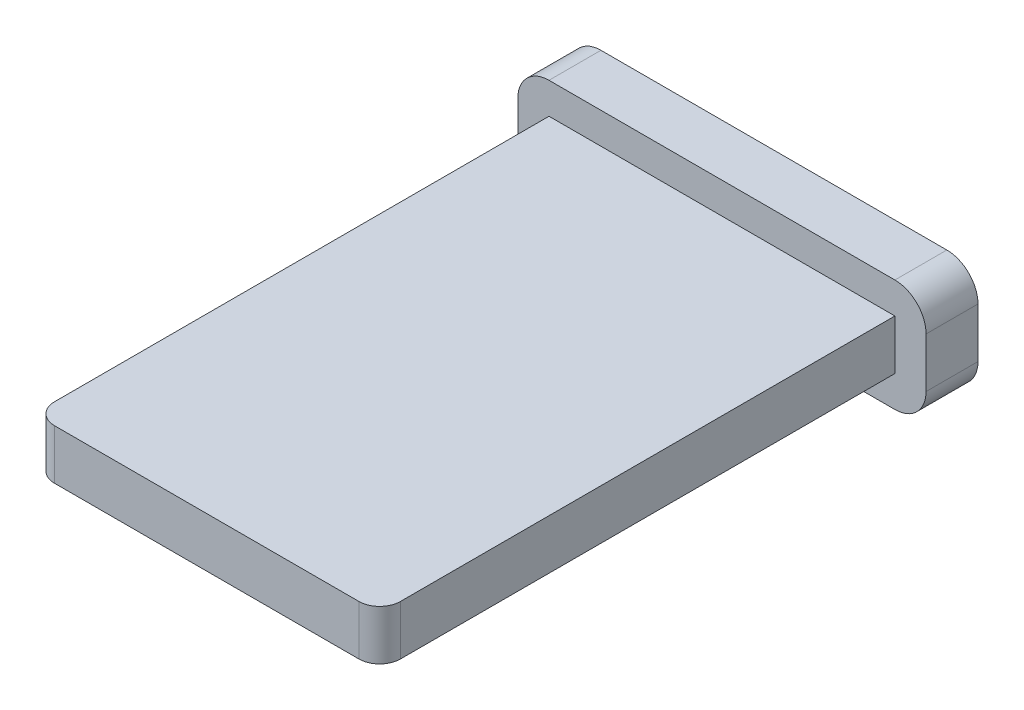
SolidWorks part; units mm, degrees
ref_plane "Front Plane" through (0, 0, 0) normal (0, 0, 1) x (1, 0, 0)
ref_plane "Top Plane" through (0, 0, 0) normal (0, 1, 0) x (1, 0, 0)
ref_plane "Right Plane" through (0, 0, 0) normal (1, 0, 0) x (0, 0, -1)
sketch "Sketch1" plane through (0, 0, 0) normal (0, 0, 1) x (1, 0, 0)
  line L1 (-16.6, 6.1019) -> (16.7, 6.1019)
  line L2 (-16.6, 6.1019) -> (-16.6, 1.3019)
  line L3 (-16.6, 1.3019) -> (16.7, 1.3019)
  line L4 (16.7, 6.1019) -> (16.7, 1.3019)
  dimension "D1" = 33.3
  dimension "D2" = 4.8
extrude "Boss-Extrude1" add sketch "Sketch1" along normal blind 49.6
fillet "Fillet1" radius 2 2 edges at (16.7, 3.7019, 49.6) (-16.6, 3.7019, 49.6)
sketch "Sketch2" plane through (0, 0, 0) normal (0, 0, -1) x (-1, 0, 0)
  line L0 (16.6, 1.3019) -> (-16.7, 1.3019) construction
  line L1 (-19.7, 9.1019) -> (19.6, 9.1019)
  line L2 (-19.7, 9.1019) -> (-19.7, -1.6981)
  line L3 (-19.7, -1.6981) -> (19.6, -1.6981)
  line L4 (19.6, 9.1019) -> (19.6, -1.6981)
  line L5 (-16.7, 6.1019) -> (16.6, 6.1019) construction
  line L6 (-16.7, 1.3019) -> (-16.7, 6.1019) construction
  line L7 (16.6, 6.1019) -> (16.6, 1.3019) construction
  dimension "D1" = 3
  dimension "D2" = 3
  dimension "D3" = 3
  dimension "D4" = 3
extrude "Boss-Extrude2" add sketch "Sketch2" along normal blind 5
fillet "Fillet2" radius 3 4 edges at (19.7, -1.6981, -2.5) (-19.6, -1.6981, -2.5) (-19.6, 9.1019, -2.5) (19.7, 9.1019, -2.5)
sketch "Sketch3" plane through (0, 0, -5) normal (0, 0, -1) x (-1, 0, 0)
  text T0 "Italo P. ISP"
extrude "Cut-Extrude1" cut sketch "Sketch3" against normal blind 2
